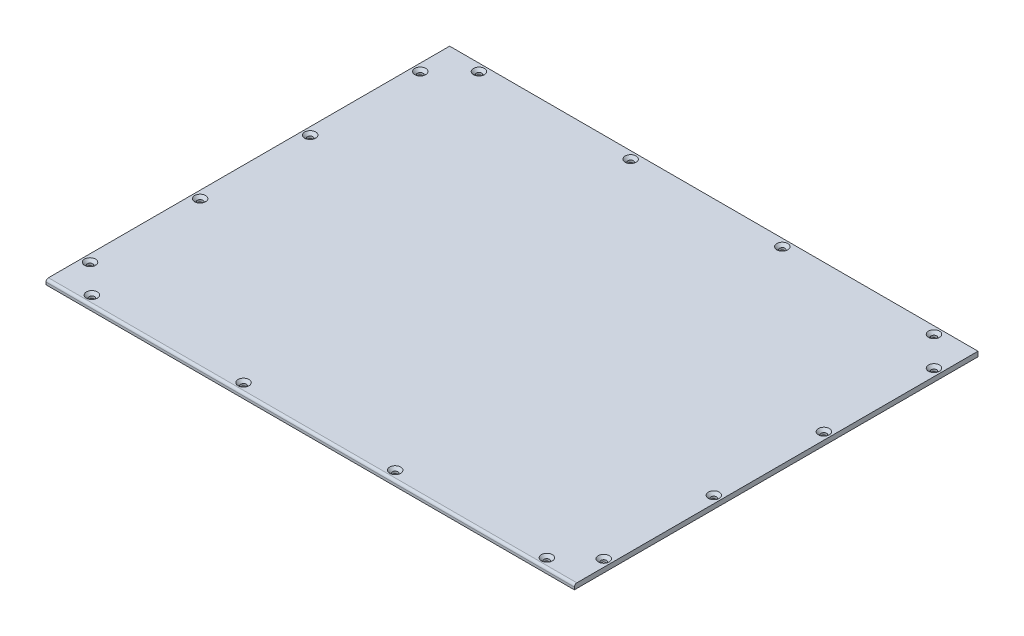
SolidWorks part; units mm, degrees
material "6061 合金"
ref_plane "前基準面" through (0, 0, 0) normal (0, 0, 1) x (1, 0, 0)
ref_plane "上基準面" through (0, 0, 0) normal (0, 1, 0) x (1, 0, 0)
ref_plane "右基準面" through (0, 0, 0) normal (1, 0, 0) x (0, 0, -1)
sketch "草圖1" plane through (0, 0, 0) normal (0, 1, 0) x (1, 0, 0)
  line L1 (0, 0) -> (432, 0)
  line L2 (0, 0) -> (0, 330)
  line L3 (0, 330) -> (432, 330)
  line L4 (432, 0) -> (432, 330)
  dimension "D1" = 432
  dimension "D2" = 330
extrude "填料-伸長1" add sketch "草圖1" along normal blind 4
hole_wizard "M4 六角凹錐坑螺釘的錐孔1" positions "草圖3" profile "草圖2" countersink size "M4" standard "Iso" end condition through all
sketch "草圖3" plane through (0, 4, 0) normal (0, 1, 0) x (1, 0, 0)
  line L0 (432, 330) -> (0, 330) construction
  line L2 (0, 330) -> (0, 0) construction
  line L3 (0, 0) -> (432, 0) construction
  line L5 (432, 0) -> (432, 330) construction
  point P0 (6, 300)
  point P2 (6, 210)
  point P4 (6, 120)
  point P6 (6, 30)
  point P8 (30, 7.5)
  point P10 (154, 7.5)
  point P12 (278, 7.5)
  point P14 (402, 7.5)
  point P16 (426, 30)
  point P18 (426, 120)
  point P20 (426, 210)
  point P22 (426, 300)
  point P24 (402, 324)
  point P26 (278, 324)
  point P28 (154, 324)
  point P30 (30, 324)
  dimension "D1" = 30
  dimension "D2" = 90
  dimension "D3" = 90
  dimension "D4" = 90
  dimension "D5" = 6
  dimension "D6" = 30
  dimension "D7" = 124
  dimension "D8" = 124
  dimension "D9" = 124
  dimension "D10" = 7.5
  dimension "D11" = 30
  dimension "D12" = 124
  dimension "D13" = 124
  dimension "D14" = 124
  dimension "D15" = 6
  dimension "D16" = 30
  dimension "D17" = 90
  dimension "D18" = 90
  dimension "D19" = 90
  dimension "D20" = 6
sketch "草圖2" plane through (6, 4, -300) normal (1, 0, 0) x (0, 0, 1)
  line L0 (0, 0) -> (0, 4)
  line L1 (0, 4) -> (2.25, 4)
  line L2 (2.25, 4) -> (2.25, 2.23)
  line L3 (2.25, 2.23) -> (4.48, 0)
  line L5 (4.48, 0) -> (0, 0)
  line L6 (-2.25, 2.23) -> (-4.48, 0) construction
  line L11 (0, -6.35) -> (0, 107.95) construction
  dimension "貫穿孔直徑" = 4.5
  dimension "貫穿孔深度" = 4
  dimension "近端錐孔直徑" = 8.96
  dimension "近端錐孔角度" = 90
fillet "圓角1" radius 2 1 edges at (216, 4, 0)
